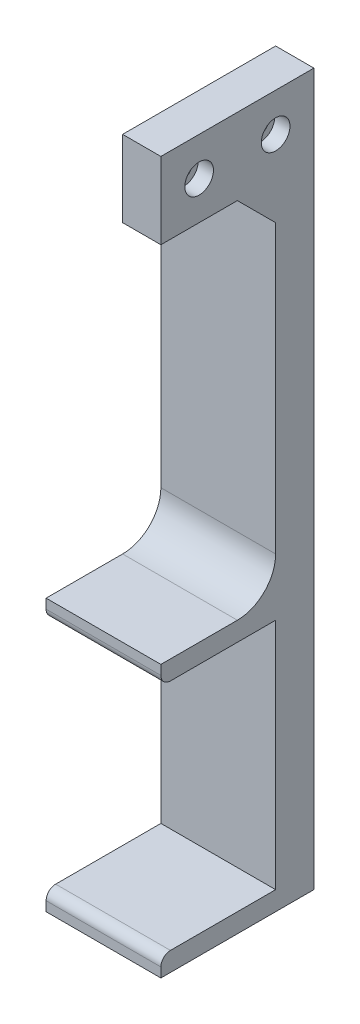
SolidWorks part; units mm, degrees
ref_plane "前基準面" through (0, 0, 0) normal (0, 0, 1) x (1, 0, 0)
ref_plane "上基準面" through (0, 0, 0) normal (0, 1, 0) x (1, 0, 0)
ref_plane "右基準面" through (0, 0, 0) normal (1, 0, 0) x (0, 0, -1)
sketch "草圖1" plane through (0, 0, 0) normal (0, 0, 1) x (1, 0, 0)
  line L1 (-11.7963, 160.3304) -> (18.2037, 160.3304)
  line L2 (-11.7963, 160.3304) -> (-11.7963, -25.6696)
  line L3 (-11.7963, -25.6696) -> (18.2037, -25.6696)
  line L4 (18.2037, 160.3304) -> (18.2037, -25.6696)
  dimension "D1" = 30
  dimension "D2" = 186
extrude "填料-伸長1" add sketch "草圖1" along normal blind 10
sketch "草圖2" plane through (0, 0, 10) normal (0, 0, 1) x (1, 0, 0)
  line L0 (18.2037, -25.6696) -> (18.2037, 160.3304) construction
  line L1 (-11.7963, -25.6696) -> (18.2037, -25.6696)
  line L2 (-11.7963, -25.6696) -> (-11.7963, -20.6696)
  line L3 (-11.7963, -20.6696) -> (18.2037, -20.6696)
  line L4 (18.2037, -25.6696) -> (18.2037, -20.6696)
  line L5 (-11.7963, 160.3304) -> (-11.7963, -25.6696) construction
  line L6 (-11.7963, 45.3304) -> (18.2037, 45.3304)
  line L7 (-11.7963, 45.3304) -> (-11.7963, 40.3304)
  line L8 (-11.7963, 40.3304) -> (18.2037, 40.3304)
  line L9 (18.2037, 45.3304) -> (18.2037, 40.3304)
  line L11 (-11.7963, 160.3304) -> (18.2037, 160.3304)
  line L12 (-11.7963, 160.3304) -> (-11.7963, 140.3304)
  line L13 (-11.7963, 140.3304) -> (18.2037, 140.3304)
  line L14 (18.2037, 160.3304) -> (18.2037, 140.3304)
  dimension "D1" = 5
  dimension "D2" = 5
  dimension "D3" = 61
  dimension "D4" = 20
extrude "填料-伸長2" add sketch "草圖2" along normal blind 30
fillet "圓角1" radius 2.5 2 edges at (3.2037, -20.6696, 40) (3.2037, 40.3304, 40)
fillet "圓角4" radius 10 1 edges at (3.2037, 45.3304, 10)
chamfer "導角7" distance 10 angle 45 1 edges at (3.2037, 140.3304, 10)
sketch "草圖3" plane through (-11.7963, 0, 0) normal (-1, 0, 0) x (0, 0, 1)
  line L0 (0, 160.3304) -> (0, -25.6696) construction
  line L1 (40, 160.3304) -> (0, 160.3304)
  line L2 (40, 160.3304) -> (40, 140.3304)
  line L3 (40, 140.3304) -> (0, 140.3304)
  line L4 (0, 160.3304) -> (0, 140.3304)
  dimension "D1" = 20
extrude "除料-伸長1" cut sketch "草圖3" against normal blind 20
sketch "草圖7" plane through (8.2037, 0, 0) normal (-1, 0, 0) x (0, 0, 1)
  line L0 (40, 160.3304) -> (0, 160.3304) construction
  line L1 (40, 140.3304) -> (40, 160.3304) construction
  line L2 (0, 160.3304) -> (0, 140.3304) construction
  circle A0 centre (30, 150.3304) radius 2.05
  circle A1 centre (10, 150.3304) radius 2.05
  dimension "D1" = 10
  dimension "D2" = 10
  dimension "D3" = 10
  dimension "D4" = 10
  dimension "D5" = 4.1
  dimension "D6" = 4.1
extrude "除料-伸長3" cut sketch "草圖7" against normal blind 10
sketch "草圖8" plane through (18.2037, 0, 0) normal (1, 0, 0) x (0, 0, -1)
  circle A0 centre (-30, 150.3304) radius 3.75
  circle A1 centre (-10, 150.3304) radius 3.75
  dimension "D1" = 7.5
  dimension "D2" = 7.5
extrude "除料-伸長4" cut sketch "草圖8" against normal blind 4
